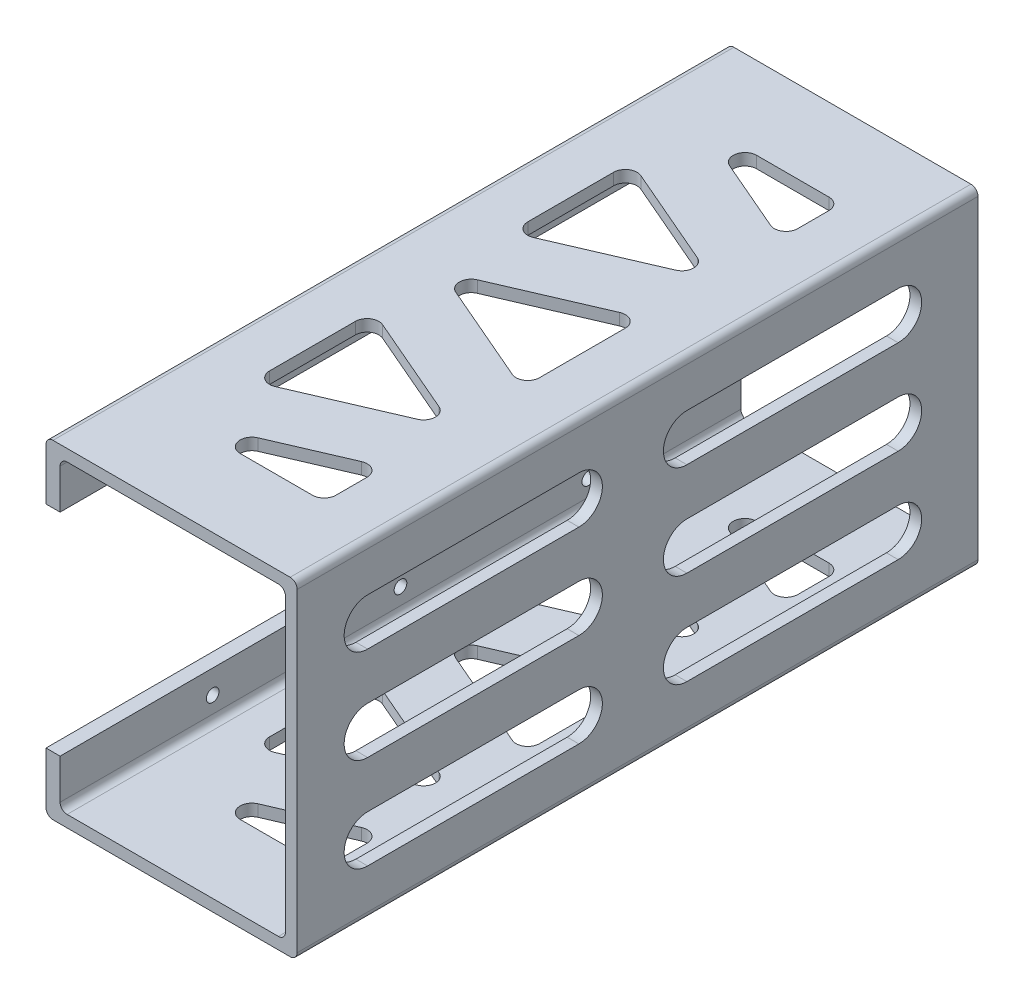
SolidWorks part; units mm, degrees
ref_plane "前视基准面" through (0, 0, 0) normal (0, 0, 1) x (1, 0, 0)
ref_plane "上视基准面" through (0, 0, 0) normal (0, 1, 0) x (1, 0, 0)
ref_plane "右视基准面" through (0, 0, 0) normal (1, 0, 0) x (0, 0, -1)
sketch "草图1" plane through (0, 0, 0) normal (0, 0, 1) x (1, 0, 0)
  line L0 (-13, -35.9663) -> (-13, -23.4663)
  line L2 (-13, -23.4663) -> (40.5, -23.4663)
  line L3 (40.5, -23.4663) -> (40.5, -93.4663)
  line L4 (40.5, -93.4663) -> (-13, -93.4663)
  line L5 (-13, -93.4663) -> (-13, -80.9663)
  line L6 (-13, -80.9663) -> (-10, -80.9663)
  line L7 (-10, -80.9663) -> (-10, -90.9663)
  line L8 (-10, -90.9663) -> (38, -90.9663)
  line L9 (38, -90.9663) -> (38, -25.9663)
  line L10 (38, -25.9663) -> (-10, -25.9663)
  line L11 (-10, -25.9663) -> (-10, -35.9663)
  line L12 (-10, -35.9663) -> (-13, -35.9663)
  dimension "D1" = 2.5
  dimension "D2" = 2.5
  dimension "D3" = 2.5
  dimension "D4" = 3
  dimension "D5" = 3
  dimension "D6" = 10
  dimension "D7" = 65
  dimension "D8" = 48
extrude "凸台-拉伸1" add sketch "草图1" against normal blind 145
sketch "草图2" plane through (-13, 0, 0) normal (-1, 0, 0) x (0, 0, 1)
  line L0 (0, -25.9663) -> (0, -90.9663) construction
  line L1 (-112.5, -30.9663) -> (-32.5, -30.9663) construction
  line L2 (-112.5, -30.9663) -> (-112.5, -85.9663) construction
  line L3 (-112.5, -85.9663) -> (-32.5, -85.9663) construction
  line L4 (-32.5, -30.9663) -> (-32.5, -85.9663) construction
  line L5 (-112.5, -30.9663) -> (-32.5, -85.9663) construction
  line L6 (-112.5, -85.9663) -> (-32.5, -30.9663) construction
  line L9 (-145, -93.4663) -> (0, -93.4663) construction
  circle A2 centre (-112.5, -30.9663) radius 1.35
  circle A3 centre (-72.5, -30.9663) radius 1.35
  circle A4 centre (-32.5, -30.9663) radius 1.35
  circle A5 centre (-32.5, -85.9663) radius 1.35
  circle A6 centre (-72.5, -85.9663) radius 1.35
  circle A7 centre (-112.5, -85.9663) radius 1.35
  point P0 (-72.5, -58.4663)
  dimension "D5" = 2.7
  dimension "D6" = 2.7
  dimension "D7" = 2.7
  dimension "D8" = 2.7
  dimension "D9" = 2.7
  dimension "D10" = 2.7
  dimension "D1" = 80
  dimension "D2" = 55
  dimension "D3" = 72.5
  dimension "D4" = 35
extrude "切除-拉伸1" cut sketch "草图2" against normal blind 3
sketch "草图3" plane through (38, 0, 0) normal (-1, 0, 0) x (0, 0, 1)
  line L0 (-128, -38.4663) -> (-83, -38.4663) construction
  line L1 (-128, -33.4663) -> (-83, -33.4663)
  line L2 (-128, -43.4663) -> (-83, -43.4663)
  line L3 (-128, -58.4663) -> (-83, -58.4663) construction
  line L4 (-128, -53.4663) -> (-83, -53.4663)
  line L5 (-128, -63.4663) -> (-83, -63.4663)
  line L6 (-128, -78.4663) -> (-83, -78.4663) construction
  line L7 (-128, -73.4663) -> (-83, -73.4663)
  line L8 (-128, -83.4663) -> (-83, -83.4663)
  line L9 (-60, -38.4663) -> (-15, -38.4663) construction
  line L10 (-60, -33.4663) -> (-15, -33.4663)
  line L11 (-60, -43.4663) -> (-15, -43.4663)
  line L12 (0, -25.9663) -> (0, -90.9663) construction
  line L13 (-128, -38.4663) -> (-15, -38.4663) construction
  line L14 (-128, -38.4663) -> (-128, -78.4663) construction
  line L15 (-128, -78.4663) -> (-15, -78.4663) construction
  line L16 (-15, -38.4663) -> (-15, -78.4663) construction
  line L17 (-145, -25.9663) -> (-145, -90.9663) construction
  line L18 (-145, -93.4663) -> (0, -93.4663) construction
  line L19 (-145, -23.4663) -> (0, -23.4663) construction
  line L20 (-60, -58.4663) -> (-15, -58.4663) construction
  line L23 (-60, -53.4663) -> (-15, -53.4663)
  line L24 (-60, -63.4663) -> (-15, -63.4663)
  line L25 (-60, -78.4663) -> (-15, -78.4663) construction
  line L26 (-60, -73.4663) -> (-15, -73.4663)
  line L27 (-60, -83.4663) -> (-15, -83.4663)
  arc A0 (-128, -33.4663) -> (-128, -43.4663) centre (-128, -38.4663) ccw
  arc A1 (-83, -43.4663) -> (-83, -33.4663) centre (-83, -38.4663) ccw
  arc A2 (-128, -53.4663) -> (-128, -63.4663) centre (-128, -58.4663) ccw
  arc A3 (-83, -63.4663) -> (-83, -53.4663) centre (-83, -58.4663) ccw
  arc A4 (-128, -73.4663) -> (-128, -83.4663) centre (-128, -78.4663) ccw
  arc A5 (-83, -83.4663) -> (-83, -73.4663) centre (-83, -78.4663) ccw
  arc A8 (-60, -33.4663) -> (-60, -43.4663) centre (-60, -38.4663) ccw
  arc A9 (-15, -43.4663) -> (-15, -33.4663) centre (-15, -38.4663) ccw
  arc A10 (-60, -53.4663) -> (-60, -63.4663) centre (-60, -58.4663) ccw
  arc A11 (-15, -63.4663) -> (-15, -53.4663) centre (-15, -58.4663) ccw
  arc A12 (-60, -73.4663) -> (-60, -83.4663) centre (-60, -78.4663) ccw
  arc A13 (-15, -83.4663) -> (-15, -73.4663) centre (-15, -78.4663) ccw
  point P2 (-105.5, -38.4663)
  point P7 (-105.5, -58.4663)
  point P14 (-105.5, -78.4663)
  point P45 (-37.5, -38.4663)
  point P53 (-37.5, -58.4663)
  point P60 (-37.5, -78.4663)
  dimension "D8" = 5
  dimension "D9" = 5
  dimension "D10" = 5
  dimension "D2" = 5
  dimension "D3" = 5
  dimension "D11" = 5
  dimension "D1" = 45
  dimension "D4" = 15
  dimension "D5" = 17
  dimension "D6" = 15
  dimension "D7" = 15
extrude "切除-拉伸2" cut sketch "草图3" against normal blind 2.5
sketch "草图4" plane through (0, -23.4663, 0) normal (0, 1, 0) x (1, 0, 0)
  line L0 (40.5, 145) -> (-13, 145) construction
  line L1 (-1.25, 127.5) -> (28.75, 127.5) construction
  line L2 (-1.25, 127.5) -> (-1.25, 17.5) construction
  line L3 (-1.25, 17.5) -> (28.75, 17.5) construction
  line L4 (28.75, 127.5) -> (28.75, 17.5) construction
  line L5 (-1.25, 112.9384) -> (4.0452, 125.2163) construction
  line L6 (40.5, 145) -> (40.5, 0) construction
  line L7 (-1.25, 87.0616) -> (4.0452, 74.7837) construction
  line L8 (28.75, 85.4384) -> (-1.25, 72.5)
  line L9 (-1.25, 72.5) -> (28.75, 59.5616)
  line L10 (-1.25, 127.5) -> (28.75, 114.5616)
  line L11 (28.75, 114.5616) -> (28.75, 127.5)
  line L12 (28.75, 127.5) -> (-1.25, 127.5)
  line L13 (-1.25, 112.9384) -> (28.75, 100)
  line L14 (28.75, 100) -> (-1.25, 87.0616)
  line L15 (-1.25, 57.9384) -> (28.75, 45)
  line L16 (28.75, 45) -> (-1.25, 32.0616)
  line L17 (-1.25, 17.5) -> (28.75, 30.4384)
  line L18 (28.75, 30.4384) -> (28.75, 17.5)
  line L19 (28.75, 17.5) -> (-1.25, 17.5)
  line L20 (-1.25, 112.9384) -> (-1.25, 87.0616)
  line L21 (28.75, 85.4384) -> (28.75, 59.5616)
  line L22 (-1.25, 57.9384) -> (-1.25, 32.0616)
  line L23 (-1.25, 57.9384) -> (4.0452, 70.2163) construction
  line L24 (-1.25, 32.0616) -> (4.0452, 19.7837) construction
  dimension "D1" = 110
  dimension "D2" = 30
  dimension "D3" = 17.5
  dimension "D4" = 11.75
extrude "切除-拉伸3" cut sketch "草图4" against normal blind 70
fillet "圆角1" radius 2.5 30 edges at (28.75, -92.2163, -17.5) (28.75, -92.2163, -30.4384) (-1.25, -92.2163, -17.5) (28.75, -92.2163, -45) (-1.25, -92.2163, -57.9384) (-1.25, -92.2163, -32.0616) (28.75, -92.2163, -59.5616) (28.75, -92.2163, -85.4384) (-1.25, -92.2163, -72.5) (-1.25, -92.2163, -87.0616) (28.75, -92.2163, -100) (-1.25, -92.2163, -112.9384) (28.75, -92.2163, -114.5616) (28.75, -92.2163, -127.5) (-1.25, -92.2163, -127.5) (28.75, -24.7163, -127.5) (28.75, -24.7163, -114.5616) (-1.25, -24.7163, -127.5) (28.75, -24.7163, -100) (-1.25, -24.7163, -112.9384) (-1.25, -24.7163, -87.0616) (28.75, -24.7163, -85.4384) (28.75, -24.7163, -59.5616) (-1.25, -24.7163, -72.5) (28.75, -24.7163, -45) (-1.25, -24.7163, -57.9384) (-1.25, -24.7163, -32.0616) (28.75, -24.7163, -30.4384) (-1.25, -24.7163, -17.5) (28.75, -24.7163, -17.5)
fillet "圆角2" radius 1.5 8 edges at (40.5, -93.4663, -72.5) (40.5, -23.4663, -72.5) (-13, -23.4663, -72.5) (-13, -93.4663, -72.5) (-10, -90.9663, -72.5) (38, -90.9663, -72.5) (38, -25.9663, -72.5) (-10, -25.9663, -72.5)
